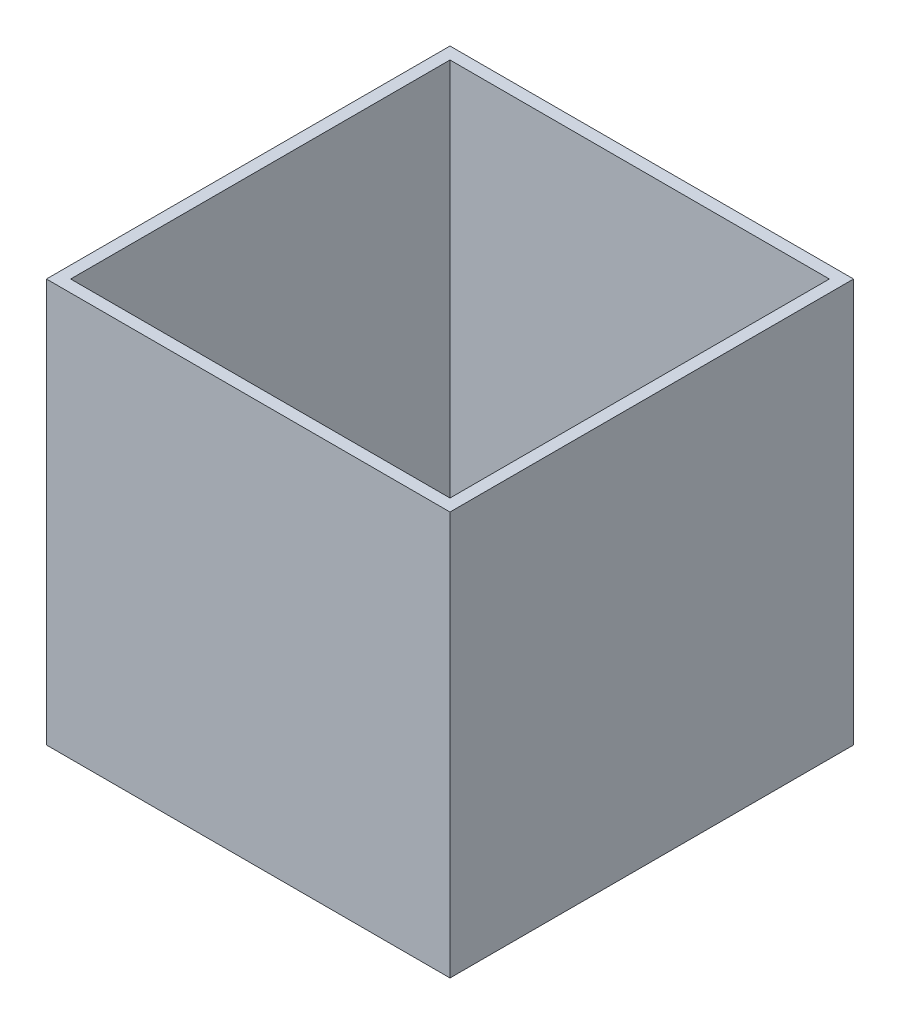
SolidWorks part; units mm, degrees
ref_plane "Front Plane" through (0, 0, 0) normal (0, 0, 1) x (1, 0, 0)
ref_plane "Top Plane" through (0, 0, 0) normal (0, 1, 0) x (1, 0, 0)
ref_plane "Right Plane" through (0, 0, 0) normal (1, 0, 0) x (0, 0, -1)
sketch "Sketch1" plane through (0, 0, 0) normal (0, 1, 0) x (1, 0, 0)
  line L1 (-89.6531, 941.6057) -> (910.3469, 941.6057)
  line L2 (-89.6531, 941.6057) -> (-89.6531, -58.3943)
  line L3 (-89.6531, -58.3943) -> (910.3469, -58.3943)
  line L4 (910.3469, 941.6057) -> (910.3469, -58.3943)
extrude "Boss-Extrude1" add sketch "Sketch1" along normal blind 1000
sketch "Sketch2" plane through (0, 1000, 0) normal (0, 1, 0) x (1, 0, 0)
  line L1 (-89.6531, 941.6057) -> (910.3469, 941.6057)
  line L2 (-89.6531, 941.6057) -> (-89.6531, -58.3943)
  line L3 (-89.6531, -58.3943) -> (910.3469, -58.3943)
  line L4 (910.3469, 941.6057) -> (910.3469, -58.3943)
shell "Shell1" thickness 30
sketch "Sketch4" plane through (0, 30, 0) normal (0, 1, 0) x (1, 0, 0)
  line L0 (-59.6531, 911.6057) -> (880.3469, -28.3943) construction
  line L1 (880.3469, -28.3943) -> (-59.6531, -28.3943) construction
  line L2 (-59.6531, -28.3943) -> (880.3469, 911.6057) construction
  line L4 (340.3469, 371.6057) -> (480.3469, 371.6057)
  line L5 (340.3469, 371.6057) -> (340.3469, 511.6057)
  line L6 (340.3469, 511.6057) -> (480.3469, 511.6057)
  line L7 (480.3469, 371.6057) -> (480.3469, 511.6057)
  line L8 (340.3469, 371.6057) -> (480.3469, 511.6057) construction
  line L9 (340.3469, 511.6057) -> (480.3469, 371.6057) construction
  point P8 (410.3469, 441.6057)
extrude "Boss-Extrude2" add sketch "Sketch4" along normal blind 200
sketch "Sketch5" plane through (480.3469, 0, 0) normal (1, 0, 0) x (0, 0, -1)
  line L1 (371.6057, 30) -> (431.6057, 30)
  line L2 (371.6057, 30) -> (371.6057, 80)
  line L3 (371.6057, 80) -> (431.6057, 80)
  line L4 (431.6057, 30) -> (431.6057, 80)
extrude "Boss-Extrude3" add sketch "Sketch5" along normal blind 20
sketch "Sketch6" plane through (0, 230, 0) normal (0, 1, 0) x (1, 0, 0)
  circle A0 centre (410.3469, 491.6057) radius 10
  circle A1 centre (360.3469, 441.6057) radius 10
  circle A2 centre (410.3469, 391.6057) radius 10
  circle A3 centre (460.3469, 441.6057) radius 10
sketch "Sketch8" plane through (0, 1000, 0) normal (0, 1, 0) x (1, 0, 0)
  line L1 (-89.6531, 941.6057) -> (910.3469, 941.6057)
  line L2 (-89.6531, 941.6057) -> (-89.6531, -58.3943)
  line L3 (-89.6531, -58.3943) -> (910.3469, -58.3943)
  line L4 (910.3469, 941.6057) -> (910.3469, -58.3943)
extrude "Cut-Extrude5" cut sketch "Sketch6" against normal blind 80
sketch "Sketch9" plane through (0, 1000, 0) normal (0, 1, 0) x (1, 0, 0)
  line L1 (910.3469, 941.6057) -> (-89.6531, 941.6057)
  line L2 (910.3469, 941.6057) -> (910.3469, -58.3943)
  line L3 (910.3469, -58.3943) -> (-89.6531, -58.3943)
  line L4 (-89.6531, 941.6057) -> (-89.6531, -58.3943)
